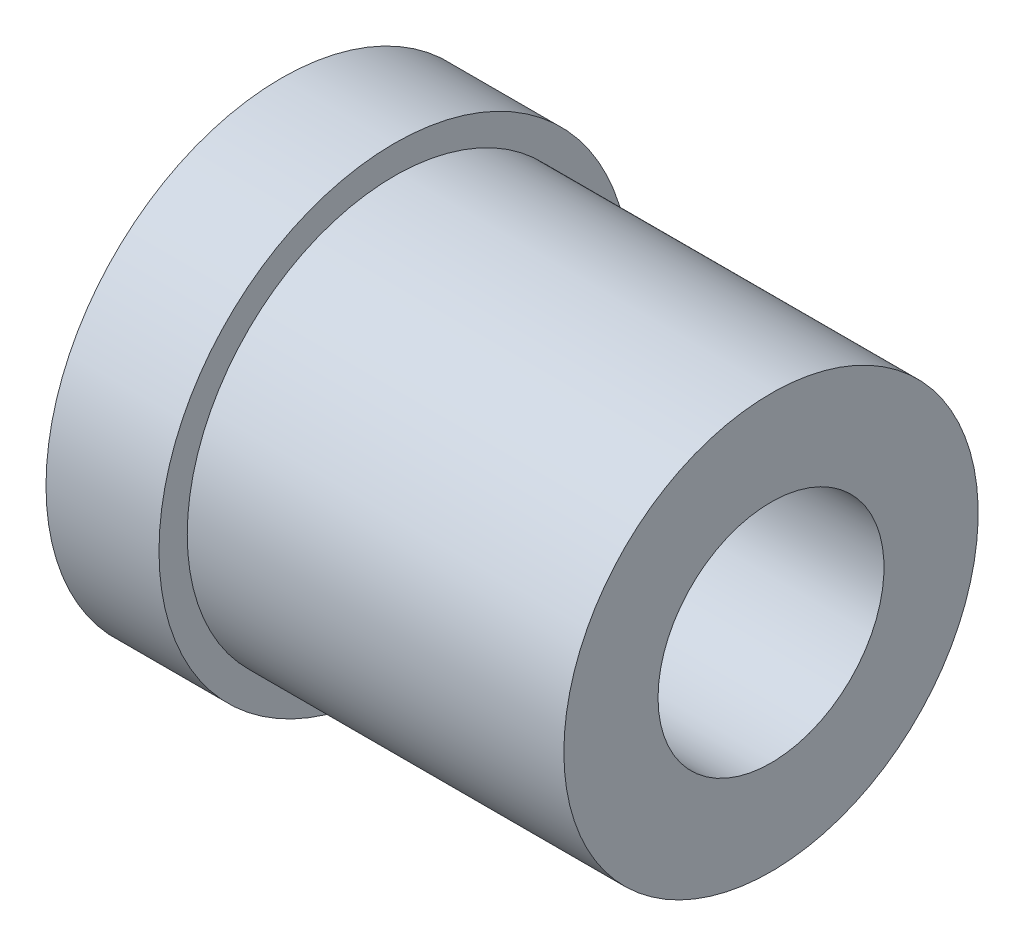
SolidWorks part; units mm, degrees
material "Сталь"
ref_plane "Спереди" through (0, 0, 0) normal (0, 0, 1) x (1, 0, 0)
ref_plane "Сверху" through (0, 0, 0) normal (0, 1, 0) x (1, 0, 0)
ref_plane "Справа" through (0, 0, 0) normal (1, 0, 0) x (0, 0, -1)
sketch "Эскиз1" plane through (0, 0, 0) normal (0, 0, 1) x (1, 0, 0)
  line L0 (0, 0) -> (40.9494, 0) construction
  line L1 (0, 12.5) -> (0, 6)
  line L2 (0, 6) -> (26, 6)
  line L3 (26, 6) -> (26, 11)
  line L4 (26, 11) -> (6, 11)
  line L5 (6, 11) -> (6, 12.5)
  line L6 (6, 12.5) -> (0, 12.5)
  dimension "D1" = 12
  dimension "D2" = 22
  dimension "D3" = 25
  dimension "D4" = 6
  dimension "D5" = 20
revolve "Повернуть1" add sketch "Эскиз1" angle 360 about L0
